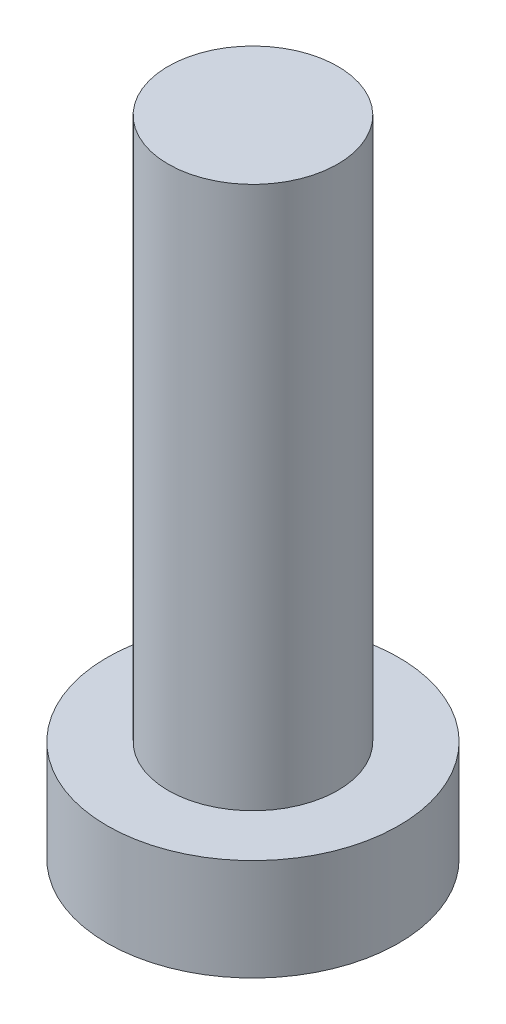
SolidWorks part; units mm, degrees
ref_plane "前视基准面" through (0, 0, 0) normal (0, 0, 1) x (1, 0, 0)
ref_plane "上视基准面" through (0, 0, 0) normal (0, 1, 0) x (1, 0, 0)
ref_plane "右视基准面" through (0, 0, 0) normal (1, 0, 0) x (0, 0, -1)
sketch "草图1" plane through (0, 0, 0) normal (0, 1, 0) x (1, 0, 0)
  circle A0 centre (0, 0) radius 4.3
extrude "凸台-拉伸1" add sketch "草图1" along normal blind 3
sketch "草图2" plane through (0, 3, 0) normal (0, 1, 0) x (1, 0, 0)
  circle A0 centre (0, 0) radius 2.5
extrude "凸台-拉伸2" add sketch "草图2" along normal blind 16
sketch "草图3" plane through (0, 0, 0) normal (0, -1, 0) x (1, 0, 0)
  line L0 (-0.6, 1.1) -> (-0.6, 2.4)
  line L1 (-2.4, -0.6) -> (-1.1, -0.6)
  line L2 (-2.4, -0.6) -> (-2.4, 0.6)
  line L3 (-2.4, 0.6) -> (-1.1, 0.6)
  line L4 (2.4, -0.6) -> (2.4, 0.6)
  line L5 (-2.4, -0.6) -> (2.4, 0.6) construction
  line L6 (-2.4, 0.6) -> (2.4, -0.6) construction
  line L7 (-0.6, -2.4) -> (0.6, -2.4)
  line L8 (-0.6, -2.4) -> (-0.6, -1.1)
  line L9 (-0.6, 2.4) -> (0.6, 2.4)
  line L10 (0.6, -2.4) -> (0.6, -1.1)
  line L11 (-0.6, -2.4) -> (0.6, 2.4) construction
  line L12 (-0.6, 2.4) -> (0.6, -2.4) construction
  line L13 (1.1, -0.6) -> (2.4, -0.6)
  line L14 (0.6, 1.1) -> (0.6, 2.4)
  line L15 (1.1, 0.6) -> (2.4, 0.6)
  arc A0 (-0.6, -1.1) -> (-1.1, -0.6) centre (-1.1, -1.1) ccw
  arc A1 (1.1, -0.6) -> (0.6, -1.1) centre (1.1, -1.1) ccw
  arc A2 (0.6, 1.1) -> (1.1, 0.6) centre (1.1, 1.1) ccw
  arc A3 (-0.6, 1.1) -> (-1.1, 0.6) centre (-1.1, 1.1) cw
  point P0 (0, 0)
  point P6 (0, 0)
  point P21 (0.6, 0.6)
  dimension "D1" = 0.5
extrude "切除-拉伸1" cut sketch "草图3" against normal blind 1.5
